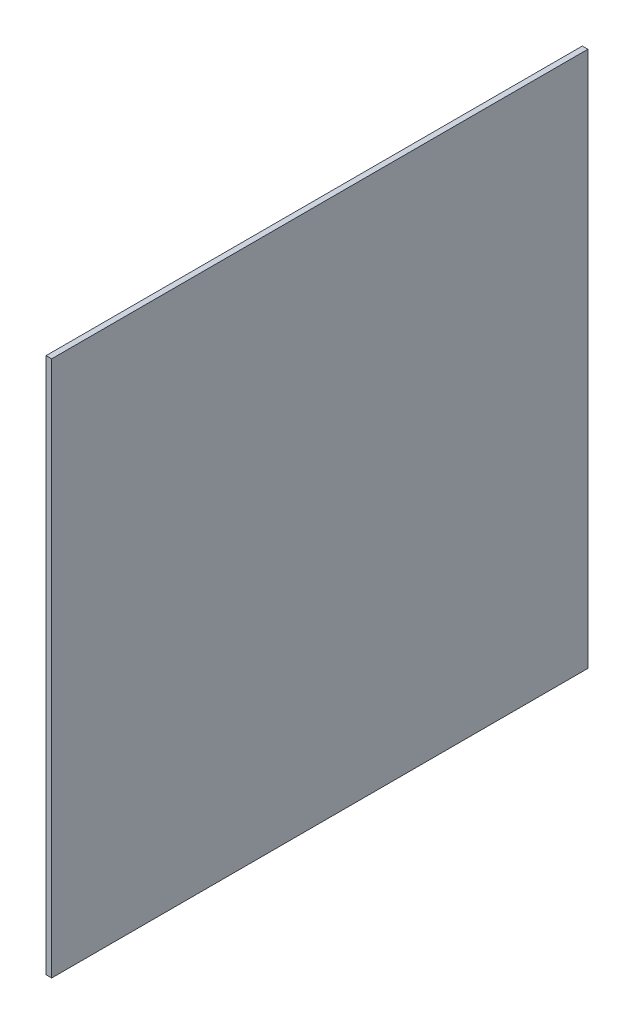
SolidWorks part; units mm, degrees
ref_plane "Front Plane" through (0, 0, 0) normal (0, 0, 1) x (1, 0, 0)
ref_plane "Top Plane" through (0, 0, 0) normal (0, 1, 0) x (1, 0, 0)
ref_plane "Right Plane" through (0, 0, 0) normal (1, 0, 0) x (0, 0, -1)
sketch "Sketch1" plane through (0, 0, 0) normal (1, 0, 0) x (0, 0, -1)
  line L1 (152.4, 152.4) -> (-152.4, 152.4)
  line L2 (152.4, 152.4) -> (152.4, -152.4)
  line L3 (152.4, -152.4) -> (-152.4, -152.4)
  line L4 (-152.4, 152.4) -> (-152.4, -152.4)
  line L5 (152.4, 152.4) -> (-152.4, -152.4) construction
  line L6 (152.4, -152.4) -> (-152.4, 152.4) construction
  point P0 (0, 0)
  dimension "D1" = 304.8
  dimension "D2" = 304.8
extrude "Boss-Extrude1" add sketch "Sketch1" along normal blind 3.175
